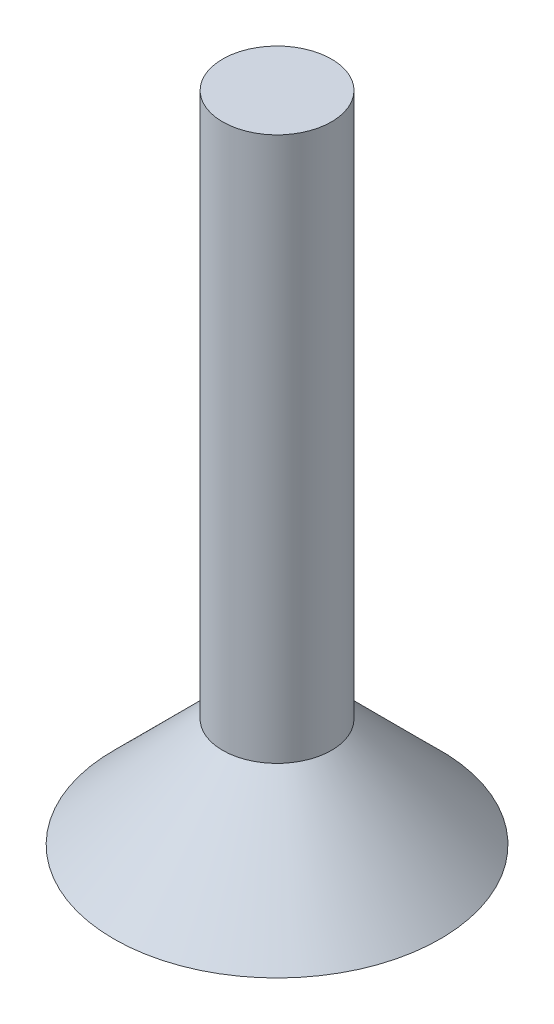
SolidWorks part; units mm, degrees
ref_plane "Спереди" through (0, 0, 0) normal (0, 0, 1) x (1, 0, 0)
ref_plane "Сверху" through (0, 0, 0) normal (0, 1, 0) x (1, 0, 0)
ref_plane "Справа" through (0, 0, 0) normal (1, 0, 0) x (0, 0, -1)
sketch "Эскиз1" plane through (0, 0, 0) normal (0, 0, 1) x (1, 0, 0)
  line L0 (0, 15) -> (1.25, 15)
  line L1 (1.25, 15) -> (1.25, 2.5)
  line L2 (1.25, 2.5) -> (3.75, 0)
  line L3 (3.75, 0) -> (0, 0)
  line L4 (0, 49.838) -> (0, -6.7101) construction
  line L5 (0, 15) -> (0, 0)
revolve "Повернуть1" add sketch "Эскиз1" angle 360 about L4
